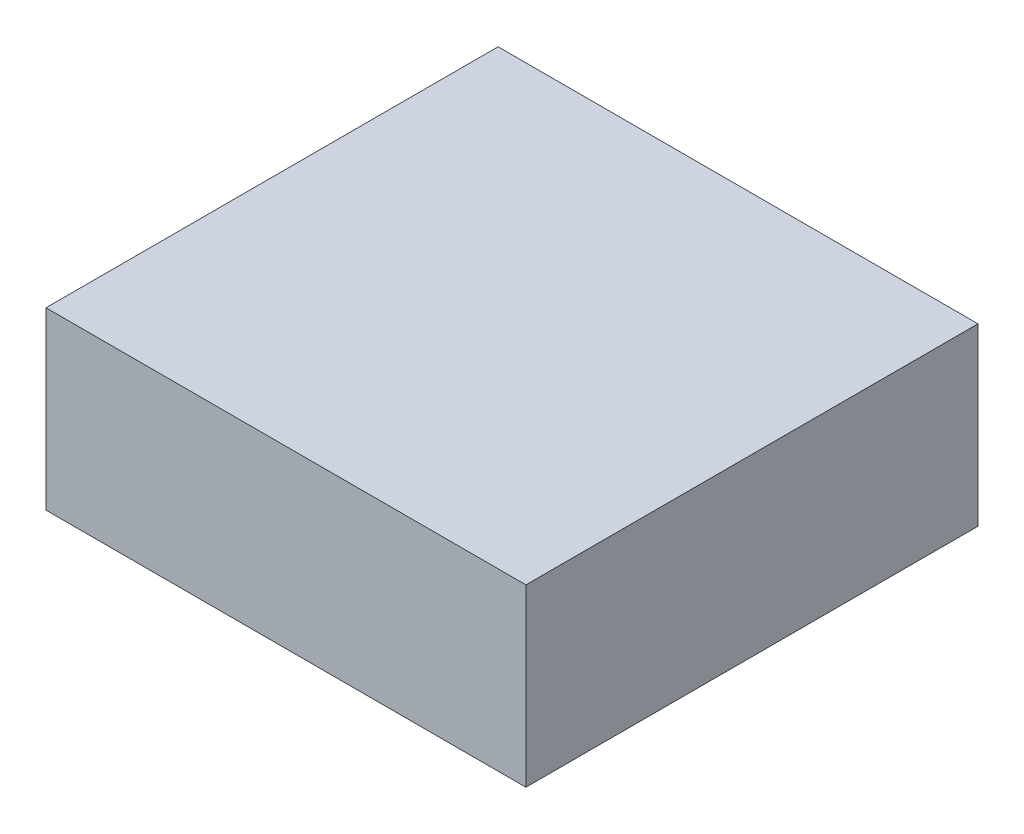
SolidWorks part; units mm, degrees
ref_plane "Front Plane" through (0, 0, 0) normal (0, 0, 1) x (1, 0, 0)
ref_plane "Top Plane" through (0, 0, 0) normal (0, 1, 0) x (1, 0, 0)
ref_plane "Right Plane" through (0, 0, 0) normal (1, 0, 0) x (0, 0, -1)
sketch "Sketch2" plane through (0, 0, 0) normal (0, 1, 0) x (1, 0, 0)
  line L1 (-17.25, 16.25) -> (17.25, 16.25)
  line L2 (-17.25, 16.25) -> (-17.25, -16.25)
  line L3 (-17.25, -16.25) -> (17.25, -16.25)
  line L4 (17.25, 16.25) -> (17.25, -16.25)
  line L5 (-17.25, 16.25) -> (17.25, -16.25) construction
  line L6 (-17.25, -16.25) -> (17.25, 16.25) construction
  point P0 (0, 0)
  dimension "D1" = 32.5
  dimension "D2" = 34.5
extrude "Boss-Extrude1" add sketch "Sketch2" along normal blind 12.6
